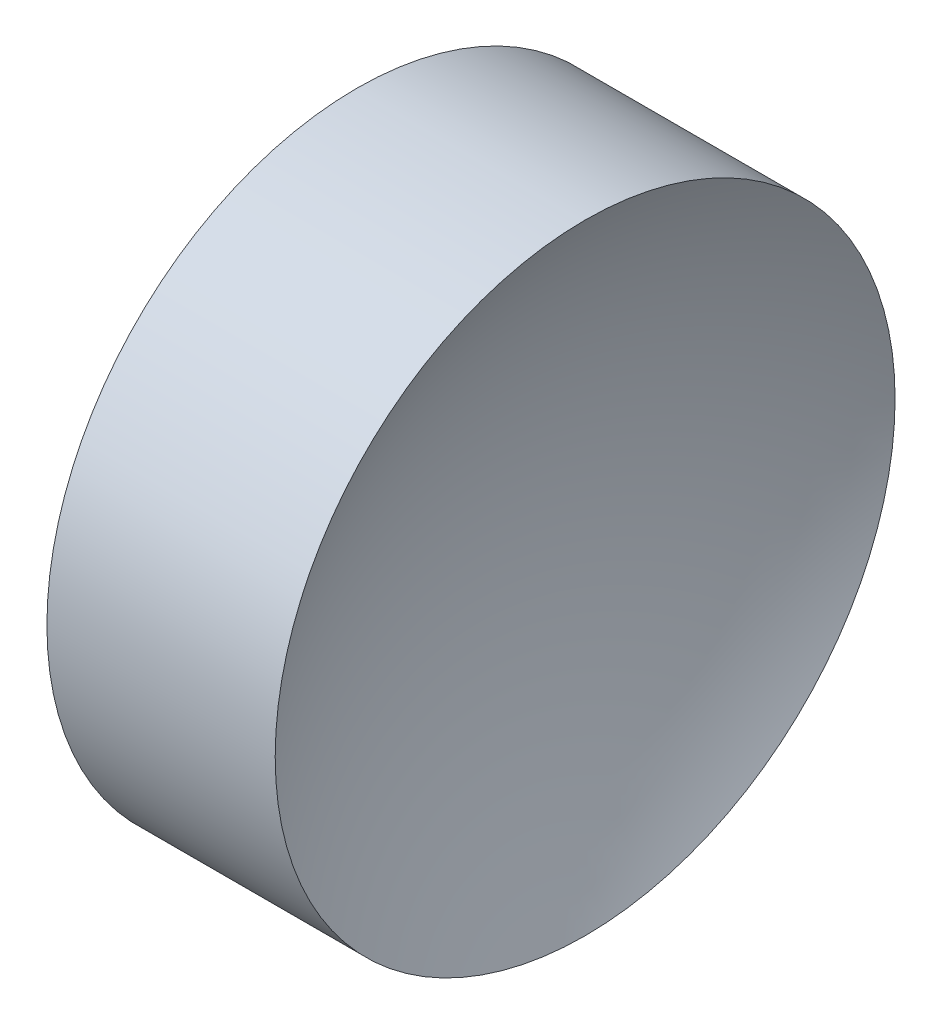
SolidWorks part; units mm, degrees
ref_plane "前视基准面" through (0, 0, 0) normal (0, 0, 1) x (1, 0, 0)
ref_plane "上视基准面" through (0, 0, 0) normal (0, 1, 0) x (1, 0, 0)
ref_plane "右视基准面" through (0, 0, 0) normal (1, 0, 0) x (0, 0, -1)
sketch "草图1" plane through (0, 0, 0) normal (0, 0, 1) x (1, 0, 0)
  line L0 (20.684, 13.0311) -> (26.997, 13.0311) construction
  line L1 (22.3093, 13.0311) -> (22.3093, 16.1811)
  line L2 (22.3093, 16.1811) -> (24.6293, 16.1811)
  line L3 (23.8093, 13.0311) -> (22.3093, 13.0311)
  arc A0 (24.6293, 16.1811) -> (23.8093, 13.0311) centre (30.2693, 13.0311) ccw
revolve "旋转1" add sketch "草图1" angle 360 about L0
